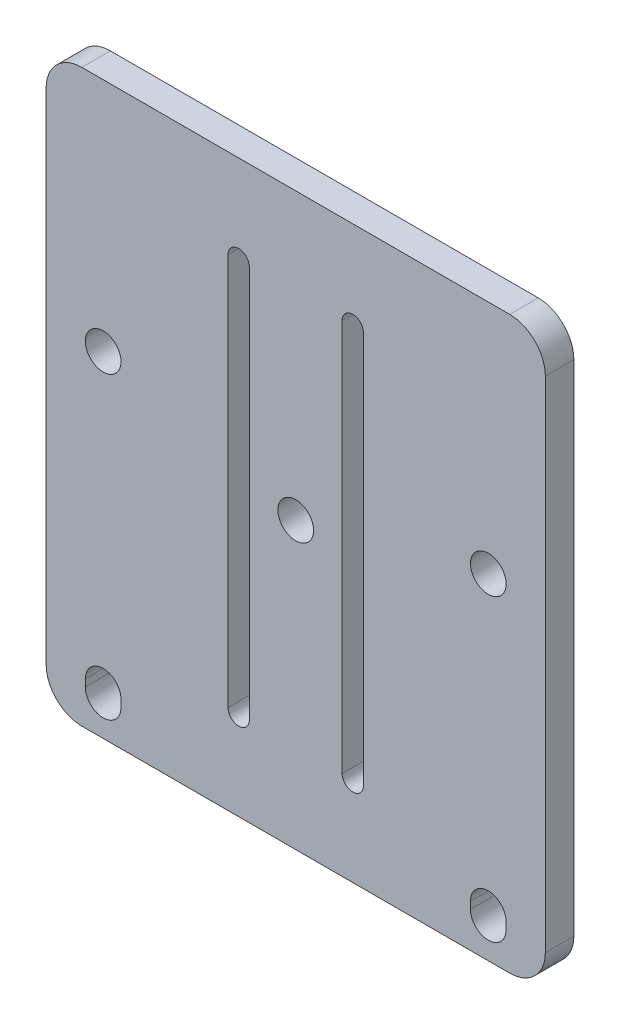
SolidWorks part; units mm, degrees
ref_plane "Front" through (0, 0, 0) normal (0, 0, 1) x (1, 0, 0)
ref_plane "Top" through (0, 0, 0) normal (0, 1, 0) x (1, 0, 0)
ref_plane "Right" through (0, 0, 0) normal (1, 0, 0) x (0, 0, -1)
sketch "Sketch4" plane through (0, 0, 0) normal (0, 0, 1) x (1, 0, 0)
  line L0 (-27, -34) -> (-27, -35) construction
  line L1 (-35, 40) -> (35, 40)
  line L2 (-35, 40) -> (-35, -40)
  line L3 (-35, -40) -> (35, -40)
  line L4 (35, 40) -> (35, -40)
  line L5 (-35, 40) -> (35, -40) construction
  line L6 (-35, -40) -> (35, 40) construction
  line L7 (-24.5, -34) -> (-24.5, -35)
  line L8 (-29.5, -34) -> (-29.5, -35)
  line L9 (0, -47.1607) -> (0, 39.6245) construction
  line L10 (27, -34) -> (27, -35) construction
  line L11 (24.5, -34) -> (24.5, -35)
  line L12 (29.5, -34) -> (29.5, -35)
  line L13 (-21.7344, 0) -> (13.0886, 0) construction
  line L14 (-15, 35) -> (15, 35) construction
  line L15 (-15, 35) -> (-15, -35) construction
  line L16 (-15, -35) -> (15, -35) construction
  line L17 (15, 35) -> (15, -35) construction
  line L18 (-15, 35) -> (15, -35) construction
  line L19 (-15, -35) -> (15, 35) construction
  circle A0 centre (-27, 7) radius 2.5
  arc A1 (-24.5, -34) -> (-29.5, -34) centre (-27, -34) ccw
  arc A2 (-29.5, -35) -> (-24.5, -35) centre (-27, -35) ccw
  arc A3 (24.5, -34) -> (29.5, -34) centre (27, -34) cw
  arc A4 (29.5, -35) -> (24.5, -35) centre (27, -35) cw
  circle A5 centre (27, 7) radius 2.5
  circle A6 centre (-15, 35) radius 1.5 construction
  circle A7 centre (15, 35) radius 1.5 construction
  circle A8 centre (15, -35) radius 1.5 construction
  circle A9 centre (-15, -35) radius 1.5 construction
  point P0 (0, 0)
  point P10 (-27, -34.5)
  point P19 (27, -34.5)
  point P28 (0, 0)
  dimension "D3" = 27
  dimension "D6" = 2.5
  dimension "D8" = 3
  dimension "D1" = 70
  dimension "D2" = 80
  dimension "D4" = 41
  dimension "D5" = 1
  dimension "D7" = 5
  dimension "D9" = 30
  dimension "D10" = 70
extrude "Boss-Extrude2" add sketch "Sketch4" along normal blind 4
fillet "Fillet1" radius 5 4 edges at (-35, -40, 2) (35, -40, 2) (35, 40, 2) (-35, 40, 2)
sketch "Sketch6" plane through (0, 0, 4) normal (0, 0, 1) x (1, 0, 0)
  line L0 (-8, 27.5) -> (-8, -27.5) construction
  line L3 (-6.5, 27.5) -> (-6.5, -27.5)
  line L4 (-9.5, 27.5) -> (-9.5, -27.5)
  line L8 (0, 19.4895) -> (0, -17.3057) construction
  line L11 (8, 27.5) -> (8, -27.5) construction
  line L15 (6.5, 27.5) -> (6.5, -27.5)
  line L18 (9.5, 27.5) -> (9.5, -27.5)
  arc A21 (-6.5, 27.5) -> (-9.5, 27.5) centre (-8, 27.5) ccw
  arc A22 (-9.5, -27.5) -> (-6.5, -27.5) centre (-8, -27.5) ccw
  arc A23 (6.5, 27.5) -> (9.5, 27.5) centre (8, 27.5) cw
  arc A24 (9.5, -27.5) -> (6.5, -27.5) centre (8, -27.5) cw
  circle A25 centre (0, 0) radius 2.5
  point P2 (-8, 0)
  point P11 (8, 0)
  dimension "D2" = 1.5
  dimension "D1" = 55
  dimension "D3" = 8
extrude "Cut-Extrude1" cut sketch "Sketch6" against normal through all
